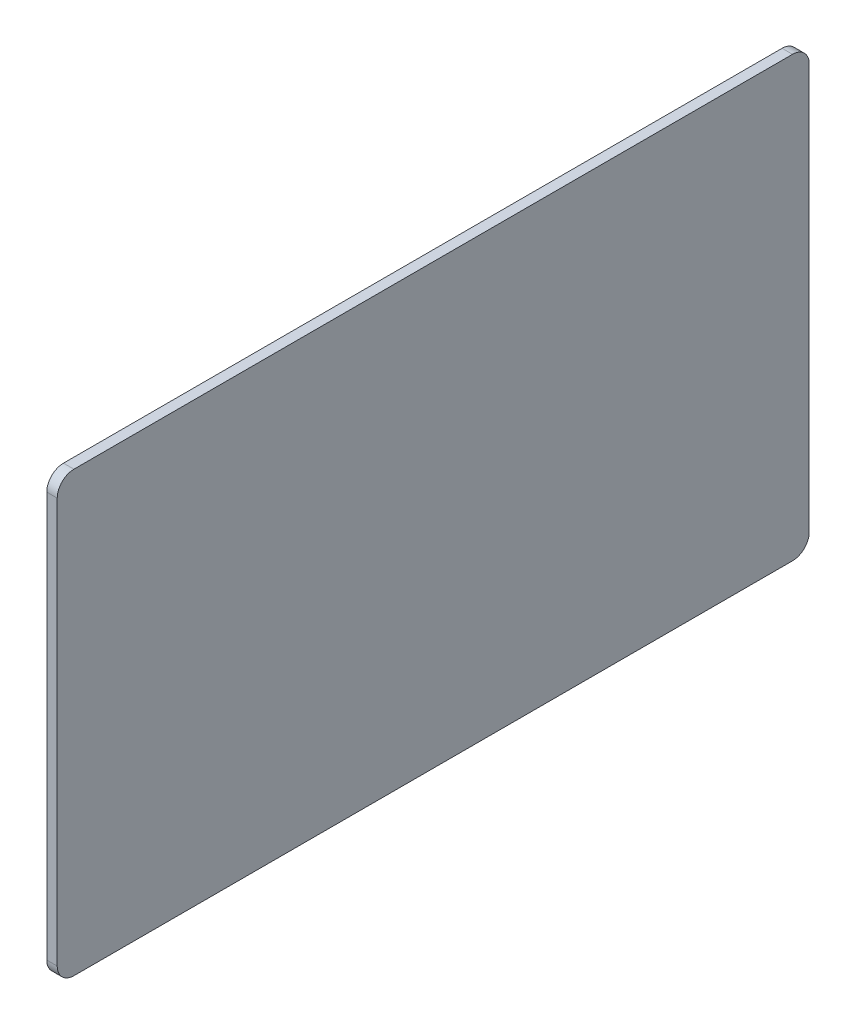
SolidWorks part; units mm, degrees
material "Acrylic (Medium-high impact)"
ref_plane "X-Y Datum" through (0, 0, 0) normal (0, 0, 1) x (1, 0, 0)
ref_plane "X-Z Datum" through (0, 0, 0) normal (0, 1, 0) x (1, 0, 0)
ref_plane "Y-Z Datum" through (0, 0, 0) normal (1, 0, 0) x (0, 0, -1)
sketch "Sketch1" plane through (0, 0, 0) normal (1, 0, 0) x (0, 0, -1)
  line L1 (-57.15, 33.3375) -> (57.15, 33.3375)
  line L2 (-57.15, 33.3375) -> (-57.15, -33.3375)
  line L3 (-57.15, -33.3375) -> (57.15, -33.3375)
  line L4 (57.15, 33.3375) -> (57.15, -33.3375)
  line L5 (-57.15, 33.3375) -> (57.15, -33.3375) construction
  line L6 (-57.15, -33.3375) -> (57.15, 33.3375) construction
  point P0 (0, 0)
  dimension "D1" = 114.3
  dimension "D2" = 66.675
extrude "Boss-Extrude1" add sketch "Sketch1" along normal blind 1.5875
fillet "Fillet1" radius 2.54 4 edges at (0.7937, -33.3375, -57.15) (0.7937, 33.3375, -57.15) (0.7937, -33.3375, 57.15) (0.7937, 33.3375, 57.15)
